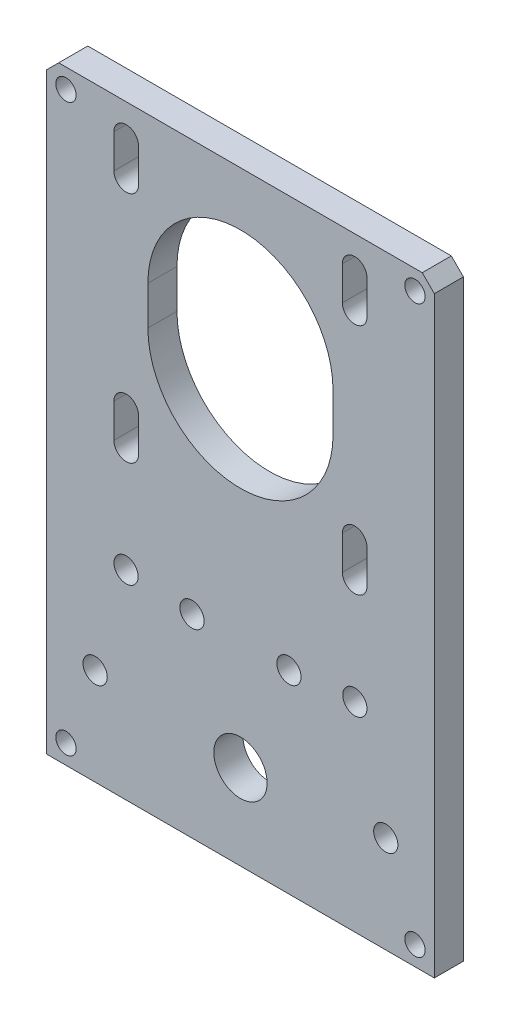
SolidWorks part; units mm, degrees
material "6061-T6 (SS)"
ref_plane "Front Plane" through (0, 0, 0) normal (0, 0, 1) x (1, 0, 0)
ref_plane "Top Plane" through (0, 0, 0) normal (0, 1, 0) x (1, 0, 0)
ref_plane "Right Plane" through (0, 0, 0) normal (1, 0, 0) x (0, 0, -1)
sketch "Sketch1" plane through (0, 0, 0) normal (0, 0, 1) x (1, 0, 0)
  line L0 (40, 124.77) -> (40, 94.58) construction
  line L1 (0, 0) -> (80, 0)
  line L2 (0, 0) -> (0, 124.77)
  line L3 (0, 124.77) -> (80, 124.77)
  line L4 (80, 0) -> (80, 124.77)
  line L5 (40, 94.58) -> (40, 86.58) construction
  line L6 (59.1, 94.58) -> (59.1, 86.58)
  line L7 (20.9, 94.58) -> (20.9, 86.58)
  line L8 (16.43, 118.15) -> (16.43, 111.15) construction
  line L9 (18.97, 118.15) -> (18.97, 111.15)
  line L10 (13.89, 118.15) -> (13.89, 111.15)
  line L11 (40, 90.58) -> (16.4656, 90.58) construction
  line L12 (63.57, 118.15) -> (63.57, 111.15) construction
  line L13 (61.03, 118.15) -> (61.03, 111.15)
  line L14 (66.11, 118.15) -> (66.11, 111.15)
  line L15 (16.43, 63.01) -> (16.43, 70.01) construction
  line L16 (18.97, 63.01) -> (18.97, 70.01)
  line L17 (13.89, 63.01) -> (13.89, 70.01)
  line L18 (63.57, 63.01) -> (63.57, 70.01) construction
  line L19 (61.03, 63.01) -> (61.03, 70.01)
  line L20 (66.11, 63.01) -> (66.11, 70.01)
  arc A0 (59.1, 94.58) -> (20.9, 94.58) centre (40, 94.58) ccw
  arc A1 (20.9, 86.58) -> (59.1, 86.58) centre (40, 86.58) ccw
  circle A2 centre (40, 17.57) radius 5.5
  arc A3 (18.97, 118.15) -> (13.89, 118.15) centre (16.43, 118.15) ccw
  arc A4 (13.89, 111.15) -> (18.97, 111.15) centre (16.43, 111.15) ccw
  arc A5 (61.03, 118.15) -> (66.11, 118.15) centre (63.57, 118.15) cw
  arc A6 (66.11, 111.15) -> (61.03, 111.15) centre (63.57, 111.15) cw
  arc A7 (18.97, 63.01) -> (13.89, 63.01) centre (16.43, 63.01) cw
  arc A8 (13.89, 70.01) -> (18.97, 70.01) centre (16.43, 70.01) cw
  arc A9 (61.03, 63.01) -> (66.11, 63.01) centre (63.57, 63.01) ccw
  arc A10 (66.11, 70.01) -> (61.03, 70.01) centre (63.57, 70.01) ccw
  point P7 (40, 90.58)
  point P17 (16.43, 114.65)
  point P26 (63.57, 114.65)
  point P33 (16.43, 66.51)
  point P40 (63.57, 66.51)
  dimension "D5" = 19.1
  dimension "D7" = 11
  dimension "D10" = 2.54
  dimension "D1" = 80
  dimension "D2" = 124.77
  dimension "D3" = 8
  dimension "D4" = 30.19
  dimension "D6" = 17.57
  dimension "D8" = 47.14
  dimension "D9" = 7
  dimension "D11" = 48.14
extrude "Boss-Extrude1" add sketch "Sketch1" along normal blind 6
hole_wizard "Ø5.0 (5) Diameter Hole1" positions "Sketch3" profile "Sketch2" hole size "Ø5.0" standard "ANSI Metric" end condition through all
sketch "Sketch3" plane through (0, 0, 6) normal (0, 0, 1) x (1, 0, 0)
  line L0 (40, 0) -> (40, -6.8027) construction
  line L1 (0, 0) -> (80, 0) construction
  point P0 (10.02, 20)
  point P2 (16.4, 41.14)
  point P4 (30, 40)
  point P13 (50, 40)
  point P14 (63.6, 41.14)
  point P15 (69.98, 20)
  dimension "D1" = 20
  dimension "D2" = 29.98
  dimension "D3" = 21.14
  dimension "D4" = 20
  dimension "D5" = 13.6
  dimension "D6" = 40
sketch "Sketch2" plane through (10.02, 20, 6) normal (1, 0, 0) x (0, -1, 0)
  line L0 (0, 0) -> (0, 6)
  line L1 (0, 6) -> (2.5, 6)
  line L2 (2.5, 6) -> (2.5, 0)
  line L5 (2.5, 0) -> (0, 0)
  line L11 (0, -6.35) -> (0, 107.95) construction
  dimension "Thru Hole Dia." = 5
  dimension "Thru Hole Depth" = 6
hole_wizard "M5x0.8 Tapped Hole1" positions "Sketch5" profile "Sketch4" tap size "M5x0.8" standard "ANSI Metric" end condition through all
sketch "Sketch5" plane through (0, 0, 6) normal (0, 0, 1) x (1, 0, 0)
  line L0 (0, 62.385) -> (40, 62.385) construction
  line L1 (0, 124.77) -> (0, 0) construction
  line L2 (40, 62.385) -> (40, 124.77) construction
  line L3 (80, 124.77) -> (0, 124.77) construction
  point P0 (4, 120.77)
  point P14 (76, 120.77)
  point P16 (76, 4)
  point P17 (4, 4)
  dimension "D1" = 72
  dimension "D2" = 116.77
sketch "Sketch4" plane through (4, 120.77, 6) normal (1, 0, 0) x (0, -1, 0)
  line L0 (0, 0) -> (0, 6)
  line L1 (0, 6) -> (2.1, 6)
  line L2 (2.1, 6) -> (2.1, 0)
  line L5 (2.1, 0) -> (0, 0)
  line L11 (0, -6.35) -> (0, 107.95) construction
  dimension "Thru Tap Drill Dia." = 4.2
  dimension "Thru Tap Drill Depth" = 6
cosmetic thread "Hole Thread1" parameters "D2"=5
cosmetic thread "Hole Thread2" parameters "D2"=5
cosmetic thread "Hole Thread3" parameters "D2"=5
cosmetic thread "Hole Thread4" parameters "D2"=5
chamfer "Chamfer1" distance 2.5 angle 45 2 edges at (0, 124.77, 3) (80, 124.77, 3)
